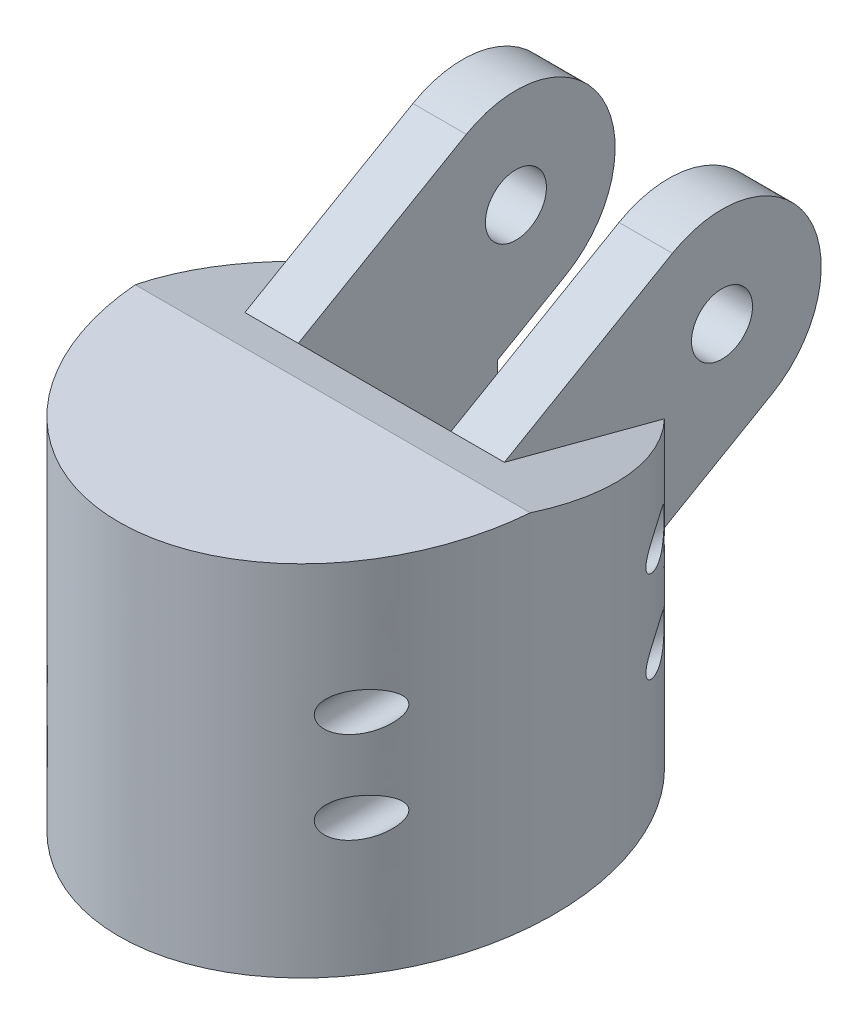
SolidWorks part; units mm, degrees
ref_plane "Front Plane" through (0, 0, 0) normal (0, 0, 1) x (1, 0, 0)
ref_plane "Top Plane" through (0, 0, 0) normal (0, 1, 0) x (1, 0, 0)
ref_plane "Right Plane" through (0, 0, 0) normal (1, 0, 0) x (0, 0, -1)
sketch "Sketch2" plane through (0, 0, 0) normal (0, 1, 0) x (1, 0, 0)
  ellipse E0 centre (0, 0) end of major axis (0, 31) minor radius 26
  dimension "D1" = 62
  dimension "D2" = 52
extrude "Boss-Extrude1" add sketch "Sketch2" along normal blind 47
sketch "Sketch3" plane through (0, 0, 0) normal (0, -1, 0) x (1, 0, 0)
  arc A0 (-12.7143, -5.8606) -> (-12.7143, 5.8606) centre (0, 0) ccw
  arc A1 (-12.7143, 5.8606) -> (-12.7143, -5.8606) centre (-14, 0) ccw
  dimension "D1" = 28
  dimension "D2" = 12
extrude "Cut-Extrude1" cut sketch "Sketch3" against normal blind 29 contours A0 A1
sketch "Sketch4" plane through (0, 0, 0) normal (1, 0, 0) x (0, 0, -1)
  line L0 (-3, 47) -> (31, 38)
  line L1 (31, 47) -> (-31, 47) construction
  line L2 (31, 0) -> (31, 47) construction
  line L3 (-3, 47) -> (31, 47)
  line L4 (31, 47) -> (31, 38)
  dimension "D1" = 34
  dimension "D2" = 9
extrude "Cut-Extrude2" cut sketch "Sketch4" against normal through all both and the other way through all
sketch "Sketch5" plane through (0, 0, 0) normal (1, 0, 0) x (0, 0, -1)
  line L0 (2.4851, 45.548) -> (24.5, 58.2583)
  line L1 (31, 38) -> (-3, 47) construction
  line L2 (37.5, 35.7417) -> (15.4851, 23.0314)
  line L4 (-3, 47) -> (5, 47) construction
  line L5 (2.4851, 45.548) -> (15.4851, 23.0314)
  arc A0 (24.5, 58.2583) -> (37.5, 35.7417) centre (31, 47) cw
  circle A1 centre (31, 47) radius 4
  dimension "D4" = 8
  dimension "D1" = 62
  dimension "D2" = 26
  dimension "D3" = 8
extrude "Boss-Extrude2" add sketch "Sketch5" along normal mid plane 34
sketch "Sketch6" plane through (0, 33.0849, 19.1016) normal (0, 0.866, 0.5) x (1, 0, 0)
  line L0 (-10, 24.9262) -> (-10, 63.3468)
  line L1 (17, 24.9262) -> (-17, 24.9262) construction
  line L2 (-10, 63.3468) -> (10, 63.3468)
  line L3 (10, 63.3468) -> (10, 24.9262)
  line L4 (10, 24.9262) -> (-10, 24.9262)
  line L5 (17, 50.3468) -> (-17, 50.3468) construction
  line L6 (17, 63.3468) -> (-17, 63.3468) construction
  point P8 (0, 50.3468)
  point P9 (0, 24.9262)
  dimension "D1" = 20
extrude "Cut-Extrude3" cut sketch "Sketch6" against normal through all
sketch "Sketch7" plane through (0, 0, 0) normal (0, 0, 1) x (1, 0, 0)
  line L0 (26, 0) -> (26, 46.2059) construction
  circle A0 centre (20, 29.8448) radius 2.5
  circle A1 centre (20, 17.8448) radius 2.5
  dimension "D2" = 5
  dimension "D1" = 12
  dimension "D3" = 6
extrude "Cut-Extrude4" cut sketch "Sketch7" against normal through all both and the other way through all
